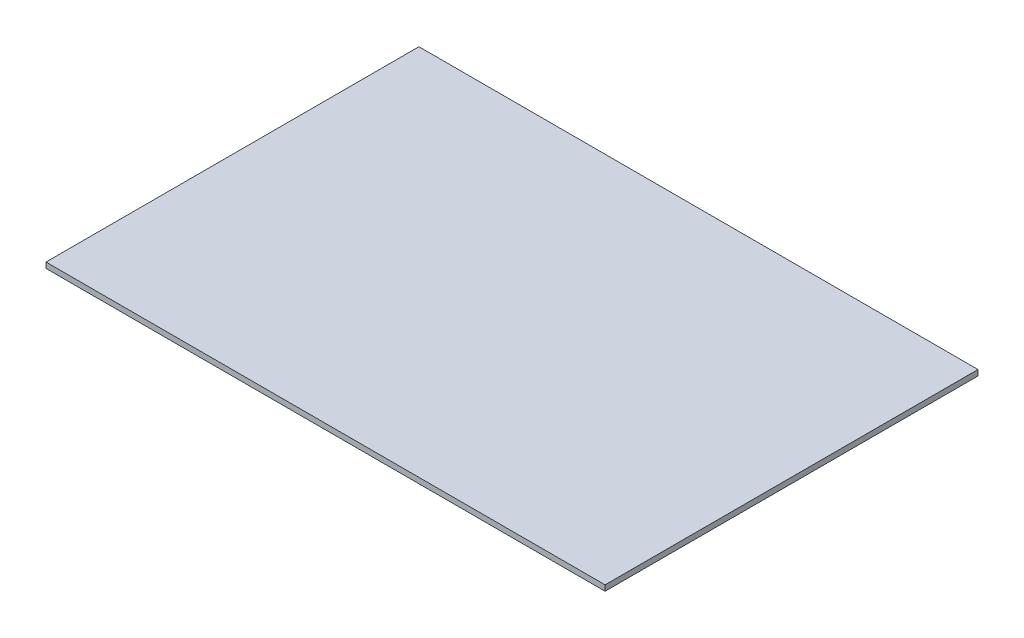
SolidWorks part; units mm, degrees
ref_plane "Face" through (0, 0, 0) normal (0, 0, 1) x (1, 0, 0)
ref_plane "Dessus" through (0, 0, 0) normal (0, 1, 0) x (1, 0, 0)
ref_plane "Droite" through (0, 0, 0) normal (1, 0, 0) x (0, 0, -1)
sketch "Esquisse1" plane through (0, 0, 0) normal (0, 1, 0) x (1, 0, 0)
  line L1 (0, 0) -> (1000, 0)
  line L2 (0, 0) -> (0, 667)
  line L3 (0, 667) -> (1000, 667)
  line L4 (1000, 0) -> (1000, 667)
  dimension "D1" = 667
  dimension "D2" = 1000
extrude "Extrusion1" add sketch "Esquisse1" along normal blind 10
